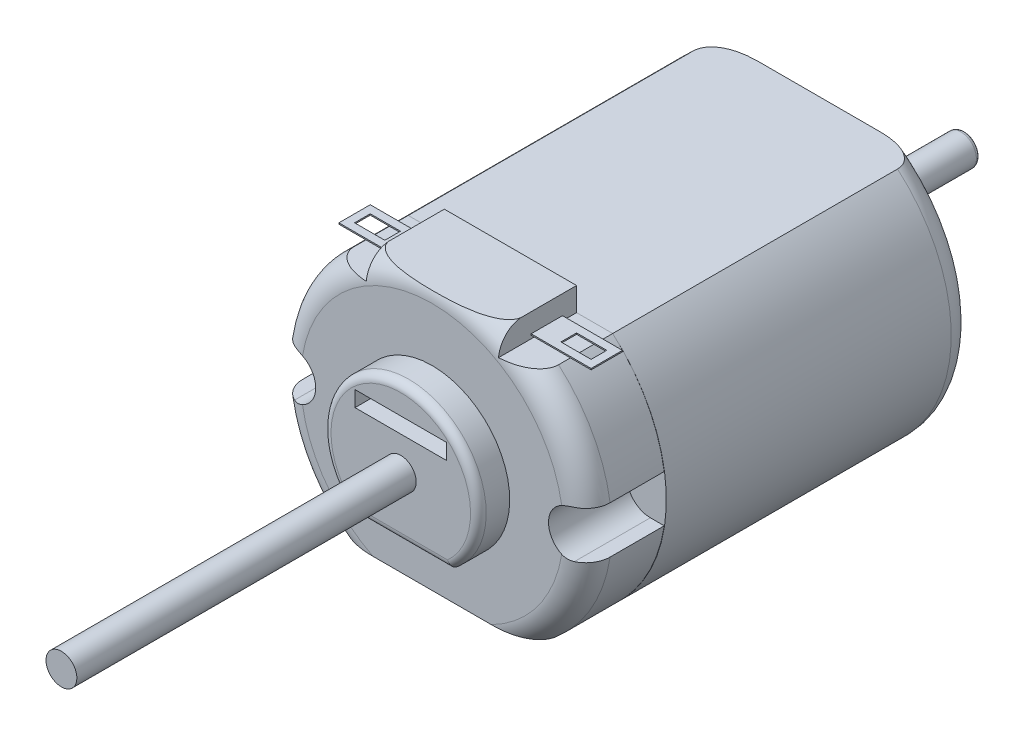
SolidWorks part; units mm, degrees
ref_plane "Front" through (0, 0, 0) normal (0, 0, 1) x (1, 0, 0)
ref_plane "Top" through (0, 0, 0) normal (0, 1, 0) x (1, 0, 0)
ref_plane "Right" through (0, 0, 0) normal (1, 0, 0) x (0, 0, -1)
sketch "Sketch1" plane through (0, 0, 0) normal (0, 0, 1) x (1, 0, 0)
  line L1 (-6.5253, -7.485) -> (6.5253, -7.485)
  line L3 (-6.5253, 7.485) -> (6.5253, 7.485)
  arc A2 (-6.5253, 7.485) -> (-6.5253, -7.485) centre (0, 0) ccw
  arc A3 (6.5253, -7.485) -> (6.5253, 7.485) centre (0, 0) ccw
  dimension "D1" = 13.0506
  dimension "D2" = 13.0506
  dimension "D3" = 9.93
extrude "Extrude1" add sketch "Sketch1" along normal blind 5
sketch "Sketch2" plane through (0, 0, 5) normal (0, 0, 1) x (1, 0, 0)
  line L3 (-3.175, -3.8015) -> (3.175, -3.8015)
  arc A0 (3.175, -3.8015) -> (-3.175, -3.8015) centre (0, 0) ccw
  dimension "D1" = 4.953
  dimension "D2" = 6.35
extrude "Extrude2" add sketch "Sketch2" along normal blind 2
sketch "Sketch4" plane through (0, 0, 5) normal (0, 0, 1) x (1, 0, 0)
  line L1 (-2.921, 3.1613) -> (2.921, 3.1621)
  line L2 (-2.921, 3.1613) -> (-2.921, 2.1621)
  line L3 (-2.921, 2.1621) -> (2.921, 2.1621)
  line L4 (2.921, 3.1621) -> (2.921, 2.1621)
  dimension "D1" = 5.842
  dimension "D2" = 1
  dimension "D3" = 2.1621
  dimension "D4" = 2.921
  dimension "D5" = 2.921
sketch "Sketch5" plane through (0, 0, 7) normal (0, 0, 1) x (1, 0, 0)
  circle A0 centre (0, 0) radius 0.985
  dimension "D1" = 1.97
extrude "Extrude3" add sketch "Sketch5" along normal blind 25
fillet "Fillet1" radius 0.25 1 edges at (0.985, 0, 32)
fillet "Fillet2" radius 0.5 2 edges at (0, -3.8015, 7) (0, 4.953, 7)
ref_plane "Plane1" through (0, 0, 0) normal (1, 0, 0) x (0, 0, -1)
sketch "Sketch6" plane through (0, 0, 5) normal (0, 0, 1) x (1, 0, 0)
  line L0 (8.93, 1.5) -> (9.8161, 1.5)
  line L1 (8.93, -1.5) -> (9.8161, -1.5)
  arc A0 (8.93, 1.5) -> (8.93, -1.5) centre (8.93, 0) ccw
  arc A1 (6.5253, -7.485) -> (6.5253, 7.485) centre (0, 0) ccw construction
  arc A2 (9.8161, -1.5) -> (9.8161, 1.5) centre (0, 0) ccw
extrude "Cut-Extrude2" cut sketch "Sketch6" against normal through all
mirror "Mirror1" about plane through (0, 0, 0) normal (1, 0, 0) of "Cut-Extrude2"
sketch "Sketch7" plane through (0, 7.485, 0) normal (0, 1, 0) x (-1, 0, 0)
  line L0 (-6.5253, 0) -> (6.5253, 0) construction
  line L1 (4.22, 5) -> (-4.22, 5)
  line L2 (4.22, 5) -> (4.22, 0)
  line L3 (4.22, 0) -> (-4.22, 0)
  line L4 (-4.22, 5) -> (-4.22, 0)
  line L5 (-6.5253, 5) -> (6.5253, 5) construction
  line L6 (0, 5) -> (0, 0) construction
  dimension "D1" = 8.44
  dimension "D2" = 4.22
extrude "Extrude4" add sketch "Sketch7" along normal blind 1.5
ref_plane "Plane2" through (0, 0, 0) normal (-0.1511, 0.9885, 0) x (-0.9885, -0.1511, 0)
sketch "Sketch8" plane through (0, 0, 0) normal (-0.1511, 0.9885, 0) x (-0.9885, -0.1511, 0)
  line L0 (9.93, 5) -> (8.1683, 3.2383) construction
  line L1 (9.4768, 5) -> (5.3198, 5) construction
  line L2 (9.93, 0) -> (9.93, 5) construction
  line L3 (0, 0) -> (0, 9.4796) construction
  line L4 (9.93, 3.4535) -> (12.3357, 3.4535)
  line L5 (8.3835, 5) -> (8.3835, 5.7279)
  line L6 (8.3835, 5.7279) -> (12.3357, 5.7279)
  line L7 (12.3357, 3.4535) -> (12.3357, 5.7279)
  arc A0 (9.93, 3.4535) -> (8.3835, 5) centre (8.3835, 3.4535) ccw
  dimension "D1" = 45
revolve "Cut-Revolve1" cut sketch "Sketch8" angle 360 about L3
sketch "Sketch9" plane through (4.22, 0, 0) normal (1, 0, 0) x (0, 0, -1)
  line L0 (-3.4535, 7.485) -> (0, 7.485) construction
  line L1 (-2.9, 7.765) -> (-0.9, 7.765)
  line L2 (-2.9, 7.765) -> (-2.9, 7.685)
  line L3 (-2.9, 7.685) -> (-0.9, 7.685)
  line L4 (-0.9, 7.765) -> (-0.9, 7.685)
  line L5 (0, 8.985) -> (0, 7.485) construction
  dimension "D1" = 2
  dimension "D2" = 0.08
  dimension "D3" = 0.2
  dimension "D4" = 0.9
extrude "Extrude5" add sketch "Sketch9" along normal blind 3.83
sketch "Sketch10" plane through (0, 7.765, 0) normal (0, 1, 0) x (-1, 0, 0)
  line L0 (-8.05, 0.9) -> (-8.05, 2.9) construction
  line L1 (-8.05, 2.9) -> (-4.22, 2.9) construction
  line L2 (-7.55, 2.4) -> (-5.62, 2.4)
  line L3 (-7.55, 2.4) -> (-7.55, 1.4)
  line L4 (-7.55, 1.4) -> (-5.62, 1.4)
  line L5 (-5.62, 2.4) -> (-5.62, 1.4)
  line L7 (-8.05, 0.9) -> (-4.22, 0.9) construction
  dimension "D1" = 1.93
  dimension "D2" = 0.5
  dimension "D3" = 0.5
  dimension "D4" = 0.5
extrude "Cut-Extrude4" cut sketch "Sketch10" against normal up to next contours L3 L4 L5 L2
sketch "Sketch21" plane through (-4.22, 0, 0) normal (-1, 0, 0) x (0, 0, 1)
  line L0 (0, 8.985) -> (0, 7.485) construction
  line L1 (0.9, 7.765) -> (2.9, 7.765)
  line L2 (0.9, 7.765) -> (0.9, 7.685)
  line L3 (0.9, 7.685) -> (2.9, 7.685)
  line L4 (2.9, 7.765) -> (2.9, 7.685)
  line L5 (3.4535, 7.485) -> (0, 7.485) construction
  dimension "D1" = 0.9
  dimension "D2" = 2
  dimension "D3" = 0.08
  dimension "D4" = 0.2
extrude "Extrude6" add sketch "Sketch21" along normal blind 3.83
sketch "Sketch22" plane through (0, 7.765, 0) normal (0, 1, 0) x (-1, 0, 0)
  line L0 (8.05, 0.9) -> (4.22, 0.9) construction
  line L1 (7.55, 1.4) -> (5.62, 1.4)
  line L2 (7.55, 1.4) -> (7.55, 2.4)
  line L3 (7.55, 2.4) -> (5.62, 2.4)
  line L4 (5.62, 1.4) -> (5.62, 2.4)
  line L5 (8.05, 2.9) -> (4.22, 2.9) construction
  line L6 (8.05, 2.9) -> (8.05, 0.9) construction
  dimension "D1" = 1.93
  dimension "D2" = 0.5
  dimension "D3" = 0.5
  dimension "D4" = 0.5
extrude "Cut-Extrude5" cut sketch "Sketch22" against normal blind 0.09
sketch "Sketch23" plane through (0, 0, 0) normal (0, 0, -1) x (-1, 0, 0)
  line L0 (-6.5253, 7.485) -> (6.5253, 7.485)
  line L1 (-6.5253, -7.485) -> (6.5253, -7.485)
  arc A0 (6.5253, 7.485) -> (6.5253, -7.485) centre (-0.0106, 0) cw
  arc A1 (-6.5253, 7.485) -> (-6.5253, -7.485) centre (-0.0593, 0) ccw
extrude "Extrude7" add sketch "Sketch23" along normal blind 19.685 separate body
fillet "Fillet6" radius 1.5 2 edges at (9.9504, 0, -19.685) (-9.9264, 0, -19.685)
sketch "Sketch26" plane through (0, 0, -19.685) normal (0, 0, -1) x (-1, 0, 0)
  circle A0 centre (0, 0) radius 3.048
  dimension "D1" = 6.096
extrude "Extrude9" add sketch "Sketch26" along normal blind 1.6002
sketch "Sketch27" plane through (0, 0, -21.2852) normal (0, 0, -1) x (-1, 0, 0)
  circle A0 centre (0, 0) radius 2.54
  dimension "D1" = 5.08
extrude "Cut-Extrude6" cut sketch "Sketch27" against normal blind 0.5334
chamfer "Chamfer1" distance 0.4 angle 20 1 edges at (-3.048, 0, -21.2852)
sketch "Sketch29" plane through (0, 0, -20.7518) normal (0, 0, -1) x (-1, 0, 0)
  circle A0 centre (0, 0) radius 0.985
  dimension "D1" = 1.97
extrude "Extrude10" add sketch "Sketch29" along normal blind 8.255
fillet "Fillet7" radius 0.25 1 edges at (-0.985, 0, -29.0068)
sketch "Sketch30" plane through (0, 0, -19.685) normal (0, 0, -1) x (-1, 0, 0)
  line L0 (-3.8522, -7.485) -> (3.8826, -7.485) construction
  circle A0 centre (0, -5.199) radius 0.7303
  dimension "D1" = 1.4605
  dimension "D2" = 2.286
extrude "Cut-Extrude7" cut sketch "Sketch30" against normal blind 8.255
extrude "Cut-Extrude9" cut sketch "Sketch4" against normal blind 5 and the other way blind 2
sketch "Sketch31" plane through (0, 0, 32) normal (0, 0, 1) x (1, 0, 0)
  circle A0 centre (0, 0) radius 2.7013
extrude "Cut-Extrude10" cut sketch "Sketch31" against normal up to surface (2.2753 mm away)
sketch "Sketch32" plane through (0, 0, 29.7247) normal (0, 0, 1) x (1, 0, 0)
  circle A0 centre (0, 0) radius 2.02
extrude "Cut-Extrude11" cut sketch "Sketch32" against normal up to surface (1.0634 mm away)
